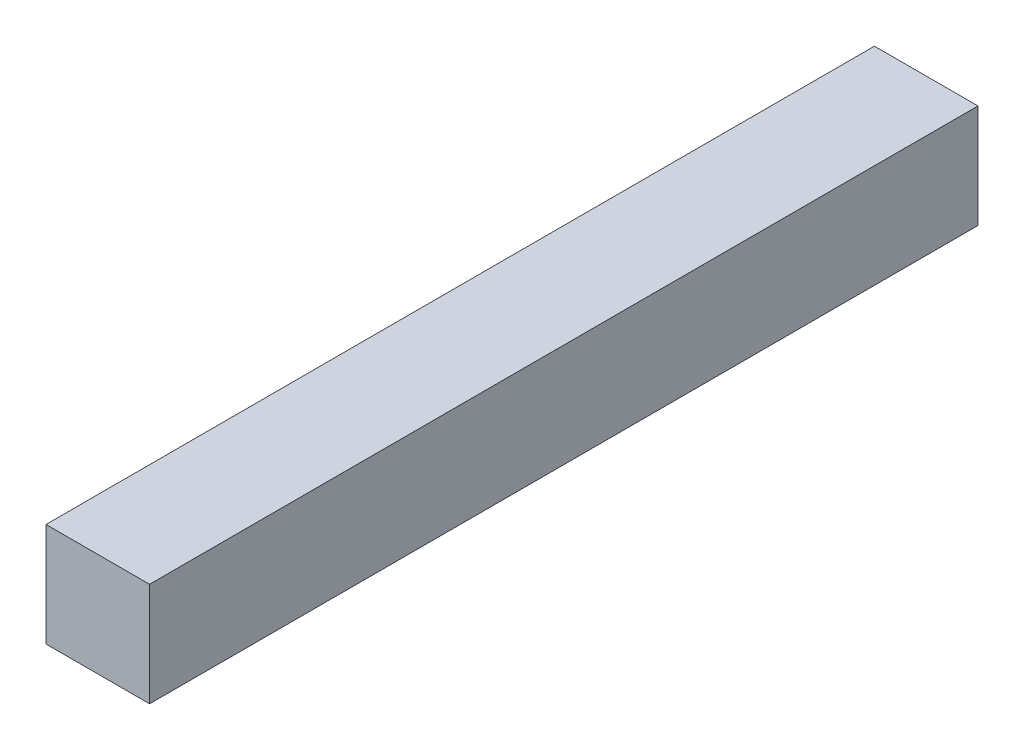
SolidWorks part; units mm, degrees
ref_plane "Front Plane" through (0, 0, 0) normal (0, 0, 1) x (1, 0, 0)
ref_plane "Top Plane" through (0, 0, 0) normal (0, 1, 0) x (1, 0, 0)
ref_plane "Right Plane" through (0, 0, 0) normal (1, 0, 0) x (0, 0, -1)
sketch "Sketch1" plane through (0, 0, 0) normal (0, 0, 1) x (1, 0, 0)
  line L1 (0, 0) -> (25.4, 0)
  line L2 (0, 0) -> (0, 25.4)
  line L3 (0, 25.4) -> (25.4, 25.4)
  line L4 (25.4, 0) -> (25.4, 25.4)
  dimension "D1" = 25.4
  dimension "D2" = 25.4
extrude "Boss-Extrude1" add sketch "Sketch1" along normal blind 203.2
